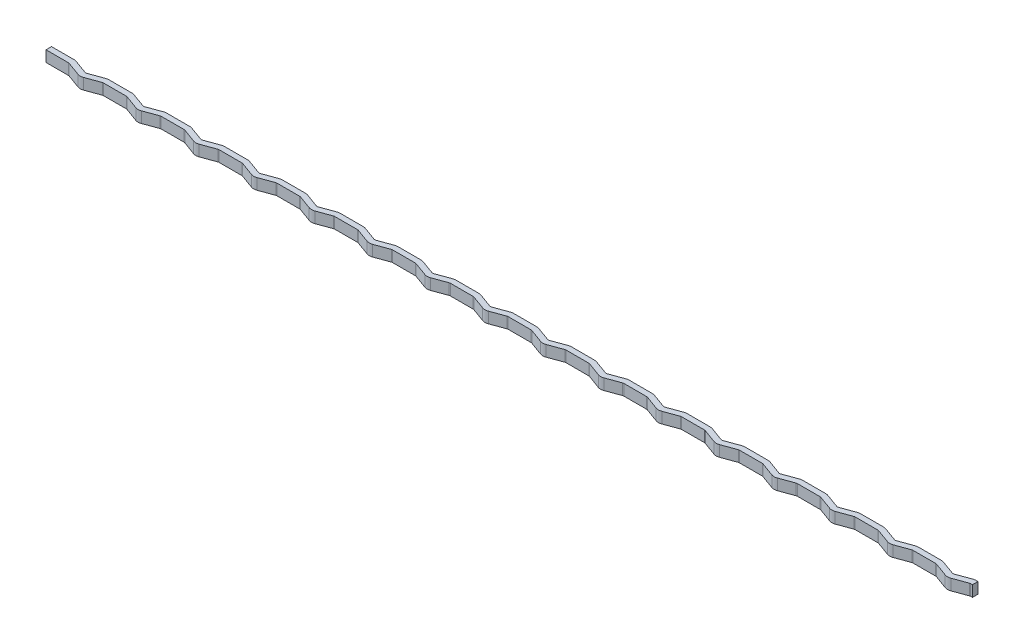
SolidWorks part; units mm, degrees
material "POLYURETHANE (11671)"
ref_plane "Front Plane" through (0, 0, 0) normal (0, 0, 1) x (1, 0, 0)
ref_plane "Top Plane" through (0, 0, 0) normal (0, 1, 0) x (1, 0, 0)
ref_plane "Right Plane" through (0, 0, 0) normal (1, 0, 0) x (0, 0, -1)
sketch "Sketch1" plane through (0, 0, 0) normal (0, 1, 0) x (1, 0, 0)
  line L0 (0, 0) -> (4.0737, 0)
  line L1 (4.25, 0) -> (10.25, 0) construction
  line L2 (7.25, 0.5445) -> (7.25, -3.0811) construction
  line L3 (10.4263, 0) -> (10.75, 0)
  line L4 (4.4157, -0.0603) -> (6.908, -0.9674)
  line L5 (7.592, -0.9674) -> (10.0843, -0.0603)
  line L6 (0, -0.5) -> (4.0737, -0.5)
  line L7 (4.2447, -0.5302) -> (6.737, -1.4373)
  line L8 (7.763, -1.4373) -> (10.2553, -0.5302)
  line L9 (10.4263, -0.5) -> (10.75, -0.5)
  line L10 (0, 0.5) -> (4.0737, 0.5)
  line L11 (4.5867, 0.4095) -> (7.079, -0.4976)
  line L12 (7.421, -0.4976) -> (9.9133, 0.4095)
  line L13 (10.4263, 0.5) -> (10.75, 0.5)
  line L14 (0, 0.5) -> (0, -0.5)
  line L15 (10.75, 0.5) -> (10.75, -0.5)
  arc A0 (4.4157, -0.0603) -> (4.0737, 0) centre (4.0737, -1) ccw
  arc A1 (10.4263, 0) -> (10.0843, -0.0603) centre (10.4263, -1) ccw
  arc A2 (7.592, -0.9674) -> (6.908, -0.9674) centre (7.25, -0.0277) cw
  arc A3 (4.2447, -0.5302) -> (4.0737, -0.5) centre (4.0737, -1) ccw
  arc A4 (7.763, -1.4373) -> (6.737, -1.4373) centre (7.25, -0.0277) cw
  arc A5 (10.4263, -0.5) -> (10.2553, -0.5302) centre (10.4263, -1) ccw
  arc A6 (4.5867, 0.4095) -> (4.0737, 0.5) centre (4.0737, -1) ccw
  arc A7 (7.421, -0.4976) -> (7.079, -0.4976) centre (7.25, -0.0277) cw
  arc A8 (10.4263, 0.5) -> (9.9133, 0.4095) centre (10.4263, -1) ccw
  point P17 (7.25, -1.0919)
  dimension "D5" = 1
  dimension "D6" = 1
  dimension "D7" = 1
  dimension "D1" = 4.25
  dimension "D2" = 6
  dimension "D3" = 0.5
  dimension "D4" = 160
  dimension "D8" = 0.5
  dimension "D9" = 0.5
extrude "Boss-Extrude1" add sketch "Sketch1" along normal blind 2 contours L10 A6 L11 A7 L12 A8 L13 L15 L9 A5 L8 A4 L7 A3 L6 L14
pattern_linear "LPattern1" count 16 spacing 10.5 along (1, 0, 0) of "Boss-Extrude1"
equation "\"OuterThickness\"= 3mm"
equation "\"MasterFillet\"= 3mm"
equation "\"PartSeperation\"= 6mm"
equation "\"D1@Sketch1\" = \"DiscThickness\" + \"LigamentExtension\" / 4"
equation "\"D2@Sketch1\"=\"PartSeperation\""
equation "\"D3@Sketch1\"=\"LigamentExtension\"/2"
equation "\"D4@Sketch1\" = 180 - \"LigamentAngle\""
equation "\"D7@Sketch1\"=\"MasterFillet\"/3"
equation "\"D6@Sketch1\"=\"MasterFillet\"/3"
equation "\"D5@Sketch1\"=\"MasterFillet\"/3"
equation "\"D9@Sketch1\" = \"LigamentDepth\" / 2"
equation "\"D8@Sketch1\" = \"LigamentDepth\" / 2"
equation "\"D1@Boss-Extrude1\" = \"LigamentThickness\""
equation "\"D3@LPattern1\"= \"DiscThickness\" + \"LigamentExtension\" / 2 + \"PartSeperation\""
equation "\"Tolerance\"= 0.15mm"
equation "\"HeightPart\"= 100mm"
equation "\"Holes\"= 1.5mm"
equation "\"SpineHolderThickness\"= 3mm"
equation "\"SpineHolderDepth\" = 3mm"
equation "\"LigamentExtension\"= 1mm"
equation "\"MotorLength\" = 40.5mm"
equation "\"MotorWidth\" = 20.3mm"
equation "\"AttachmentHeight\"= 3mm"
equation "\"SpoolDiameter\"= 60mm"
equation "\"SpoolHeight\"= 2mm"
equation "\"SpoolRidgeHeight\"= 1mm"
equation "\"SpoolRidgeDepth\"= 2mm"
equation "\"SpoolSeperation\"= 2mm"
equation "\"ServoHolderWidthOffset\"= 20mm"
equation "\"MotorTransmitterToScrew\"= 21.7mm"
equation "\"SpoolToSpine\"= 15mm"
equation "\"SpoolCenterToMotor\" = 31.5mm"
equation "\"HubOffset\"= 18mm"
equation "\"ServoFastenerHolders\"=2mm"
equation "\"ArduinoLength\" = 53.4mm"
equation "\"ArduinoWidth\" = 50mm"
equation "\"ArdYOffset\" = 29.5mm"
equation "\"ArdXOffset\" = 20.5mm"
equation "\"ArdXOffsetSmall\" = 25mm"
equation "\"MiddleServoOffset\"= 12mm"
equation "\"LargeServoOffset\"= 3mm"
equation "\"SmallServoOffset\"= 0mm"
equation "\"ToolHoleDiameter\"= 12mm"
equation "\"DiscThickness\"= 4mm"
equation "\"LigamentThickness\"= 2mm"
equation "\"LigamentAngle\"= 20deg"
equation "\"SpineDiameter\"= 15mm"
equation "\"LigamentDepth\"= 1mm"
equation "\"NoOfSegments\"= 3"
equation "\"DisksInSegments\"= 5"
equation "\"D1@LPattern1\"=\"NoOfSegments\"*\"DisksInSegments\"+1"
equation "\"TendonExtension\" = 1mm"
